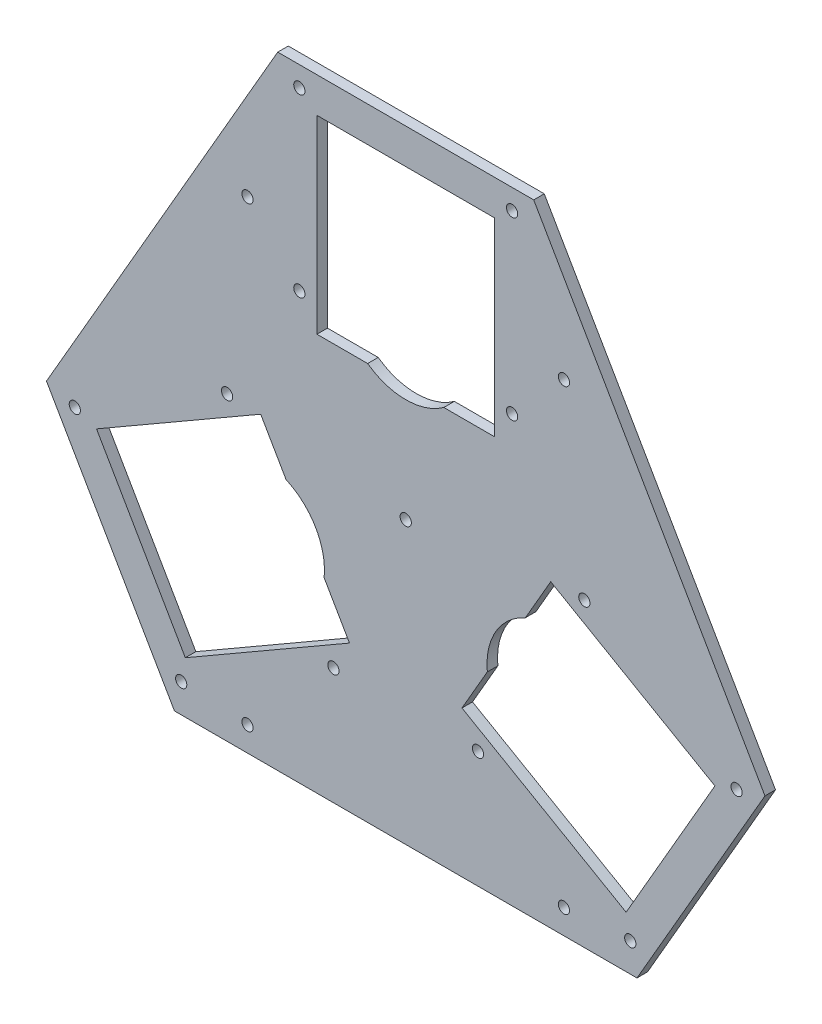
SolidWorks part; units mm, degrees
ref_plane "正面" through (0, 0, 0) normal (0, 0, 1) x (1, 0, 0)
ref_plane "平面" through (0, 0, 0) normal (0, 1, 0) x (1, 0, 0)
ref_plane "右側面" through (0, 0, 0) normal (1, 0, 0) x (0, 0, -1)
sketch "ｽｹｯﾁ1" plane through (0, 0, 0) normal (0, 0, 1) x (1, 0, 0)
  line L0 (0, -1.65) -> (0, 1.65) construction
  line L1 (-25.25, 86.9554) -> (25.25, 86.9554)
  line L2 (-25.25, 86.9554) -> (-25.25, 33.0446)
  line L3 (-25.25, 33.0446) -> (25.25, 33.0446) construction
  line L4 (25.25, 86.9554) -> (25.25, 33.0446)
  line L5 (-25.25, 86.9554) -> (25.25, 33.0446) construction
  line L6 (-25.25, 33.0446) -> (25.25, 86.9554) construction
  line L7 (0, 60) -> (0, 0) construction
  line L9 (30.25, 91.1955) -> (30.25, 41.1955) construction
  line L10 (-30.25, 91.1955) -> (-30.25, 41.1955) construction
  line L11 (87.9306, -21.6106) -> (62.6806, -65.3449)
  line L12 (87.9306, -21.6106) -> (41.2424, 5.3449)
  line L13 (62.6806, -65.3449) -> (15.9924, -38.3894)
  line L14 (41.2424, 5.3449) -> (15.9924, -38.3894) construction
  line L15 (87.9306, -21.6106) -> (15.9924, -38.3894) construction
  line L16 (41.2424, 5.3449) -> (62.6806, -65.3449) construction
  line L17 (51.9615, -30) -> (0, 0) construction
  line L18 (94.1026, -19.4005) -> (50.8013, 5.5995) construction
  line L19 (63.8526, -71.795) -> (20.5513, -46.795) construction
  line L20 (-62.6806, -65.3449) -> (-87.9306, -21.6106)
  line L21 (-62.6806, -65.3449) -> (-15.9924, -38.3894)
  line L22 (-87.9306, -21.6106) -> (-41.2424, 5.3449)
  line L23 (-15.9924, -38.3894) -> (-41.2424, 5.3449) construction
  line L24 (-62.6806, -65.3449) -> (-41.2424, 5.3449) construction
  line L25 (-15.9924, -38.3894) -> (-87.9306, -21.6106) construction
  line L26 (-51.9615, -30) -> (0, 0) construction
  line L27 (-63.8526, -71.795) -> (-20.5513, -46.795) construction
  line L28 (-94.1026, -19.4005) -> (-50.8013, 5.5995) construction
  line L29 (1.65, 0) -> (-1.65, 0) construction
  line L30 (-36.3988, 96.9554) -> (36.3988, 96.9554)
  line L31 (0, 160) -> (-138.5641, -80) construction
  line L32 (-138.5641, -80) -> (138.5641, -80) construction
  line L33 (138.5641, -80) -> (0, 160) construction
  line L34 (36.3988, 96.9554) -> (102.1653, -16.9554)
  line L35 (102.1653, -16.9554) -> (65.7665, -80)
  line L36 (65.7665, -80) -> (-65.7665, -80)
  line L37 (-65.7665, -80) -> (-102.1653, -16.9554)
  line L38 (-102.1653, -16.9554) -> (-36.3988, 96.9554)
  line L39 (-25.25, 33.0446) -> (25.25, 33.0446)
  line L40 (-45, -73) -> (45, -73) construction
  line L41 (-45, -73) -> (-45, 57) construction
  line L42 (-45, 57) -> (45, 57) construction
  line L43 (45, -73) -> (45, 57) construction
  line L44 (-45, -73) -> (45, 57) construction
  line L45 (-45, 57) -> (45, -73) construction
  line L46 (41.2424, 5.3449) -> (15.9924, -38.3894)
  line L47 (-15.9924, -38.3894) -> (-41.2424, 5.3449)
  circle A0 centre (30.25, 91.1955) radius 1.6
  circle A1 centre (30.25, 41.1955) radius 1.6
  circle A2 centre (-30.25, 41.1955) radius 1.6
  circle A3 centre (-30.25, 91.1955) radius 1.6
  circle A4 centre (63.8526, -71.795) radius 1.6
  circle A5 centre (94.1026, -19.4005) radius 1.6
  circle A6 centre (50.8013, 5.5995) radius 1.6
  circle A7 centre (20.5513, -46.795) radius 1.6
  circle A8 centre (-94.1026, -19.4005) radius 1.6
  circle A9 centre (-63.8526, -71.795) radius 1.6
  circle A10 centre (-20.5513, -46.795) radius 1.6
  circle A11 centre (-50.8013, 5.5995) radius 1.6
  circle A12 centre (0, 0) radius 80 construction
  circle A13 centre (-45, 57) radius 1.6
  circle A14 centre (45, 57) radius 1.6
  circle A15 centre (45, -73) radius 1.6
  circle A16 centre (-45, -73) radius 1.6
  circle A17 centre (0, 0) radius 1.6
  point P0 (0, 60)
  point P19 (30.25, 66.1955)
  point P46 (0, 0)
  point P48 (0, -80)
  point P59 (0, -8)
  point P76 (0, 0)
  dimension "D1" = 3.2
  dimension "D12" = 3.2
  dimension "D17" = 3.2
  dimension "D2" = 50.5
  dimension "D3" = 53.9109
  dimension "D4" = 50
  dimension "D5" = 5
  dimension "D6" = 60
  dimension "D8" = 66.1955
  dimension "D9" = 80
  dimension "D10" = 10
  dimension "D11" = 8
  dimension "D13" = 130
  dimension "D14" = 90
  dimension "D15" = 0
  dimension "D7" = 3
  dimension "D16" = 3
extrude "ﾎﾞｽ - 押し出し1" add sketch "ｽｹｯﾁ1" along normal blind 3
sketch "ｽｹｯﾁ2" plane through (0, 0, 3) normal (0, 0, 1) x (1, 0, 0)
  line L0 (-25.25, 33.0446) -> (25.25, 33.0446) construction
  line L1 (-10.8282, 33.0446) -> (10.8282, 33.0446)
  line L4 (34.0315, -7.1448) -> (23.2033, -25.8998)
  line L5 (-23.2033, -25.8998) -> (-34.0315, -7.1448)
  arc A0 (-10.8282, 33.0446) -> (10.8282, 33.0446) centre (0, 48.0446) ccw
  arc A3 (34.0315, -7.1448) -> (23.2033, -25.8998) centre (41.6078, -24.0223) ccw
  arc A4 (-23.2033, -25.8998) -> (-34.0315, -7.1448) centre (-41.6078, -24.0223) ccw
  point P13 (-0.2887, 0.5)
  point P14 (0, 0)
  dimension "D1" = 18.5
  dimension "D2" = 15
  dimension "D3" = 3
extrude "ｶｯﾄ - 押し出し1" cut sketch "ｽｹｯﾁ2" against normal through all
equation "\"D3@ｽｹｯﾁ1\"=39/sin(50)+3"
equation "\"D8@ｽｹｯﾁ1\"=\"D6@ｽｹｯﾁ1\"+5/tan(50)+2"
